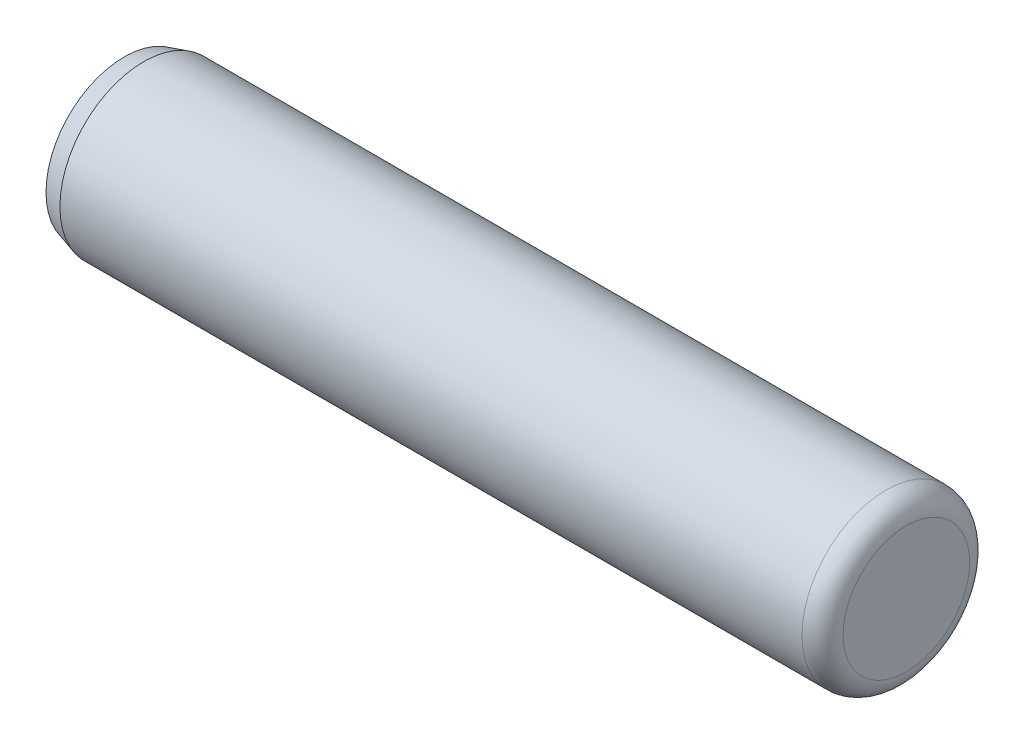
SolidWorks part; units mm, degrees
ref_plane "Front" through (0, 0, 0) normal (0, 0, 1) x (1, 0, 0)
ref_plane "Top" through (0, 0, 0) normal (0, 1, 0) x (1, 0, 0)
ref_plane "Right" through (0, 0, 0) normal (1, 0, 0) x (0, 0, -1)
sketch "Sketch1" plane through (0, 0, 0) normal (1, 0, 0) x (0, 0, -1)
  circle A0 centre (0, 0) radius 2.3813 construction
  point P3 (0, 2.3813)
  dimension "Diameter" = 4.7625
sketch "Sketch2" plane through (0, 0, 0) normal (0, 0, 1) x (1, 0, 0)
  line L0 (-11.1125, 0) -> (11.1125, 0) construction
  line L1 (11.1125, 1.797) -> (11.1125, -0.6481) construction
  line L2 (-11.1125, 2.2225) -> (-11.1125, -2.2225) construction
  line L3 (-11.1125, 2.2225) -> (-11.1125, 2.3813) construction
  line L4 (-11.1125, -2.2225) -> (-11.1125, -2.3813) construction
  line L5 (-11.1125, 2.2225) -> (-10.5589, 2.3813) construction
  line L6 (-10.5589, 2.3813) -> (10.5283, 2.3812) construction
  arc A0 (10.5283, 2.3812) -> (11.1125, 1.797) centre (10.5283, 1.7971) cw construction
  point P6 (-6.35, 0)
  point P8 (6.35, 0)
  point P23 (9.5377, 2.3813)
  dimension "Crown Radius" = 0.5842
  dimension "Length" = 22.225
  dimension "D1" = 4.7625
  dimension "D2" = 4.7625
  dimension "Point Diameter" = 4.445
  dimension "D3" = 16
  dimension "Crown Height" = 1.5748
sketch "Sketch3" plane through (0, 0, 0) normal (0, 0, 1) x (1, 0, 0)
  line L0 (11.1125, 1.797) -> (11.1125, -0.6481) construction
  line L1 (-10.5589, 2.3813) -> (10.5283, 2.3812) construction
  line L2 (-11.1125, 2.2225) -> (-10.5589, 2.3813) construction
  line L3 (-11.1125, 2.2225) -> (-11.1125, -2.2225) construction
  line L4 (-11.1125, 0) -> (11.1125, 0) construction
  line L5 (11.1125, 1.797) -> (11.1125, 0)
  line L6 (-10.5589, 2.3813) -> (10.5283, 2.3812)
  line L7 (-11.1125, 2.2225) -> (-10.5589, 2.3813)
  line L8 (-11.1125, 2.2225) -> (-11.1125, 0)
  line L9 (-11.1125, 0) -> (11.1125, 0)
  arc A0 (11.1125, 1.797) -> (10.5283, 2.3812) centre (10.5283, 1.7971) ccw construction
  arc A1 (11.1125, 1.797) -> (10.5283, 2.3812) centre (10.5283, 1.7971) ccw
revolve "Revolve1" add sketch "Sketch3" angle 360 about L0
equation "\"D1@Sketch2\" = \"Diameter@Sketch1\""
equation "\"D2@Sketch2\" = \"Diameter@Sketch1\""
